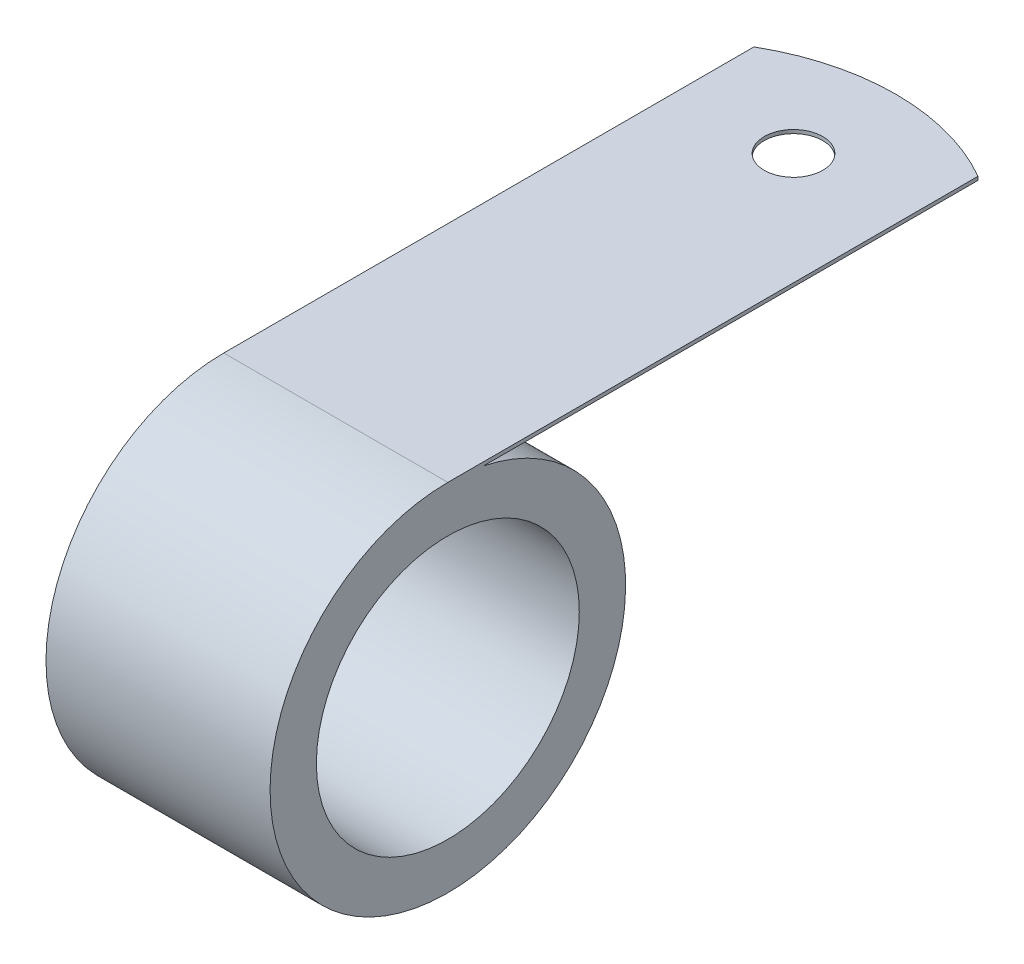
SolidWorks part; units mm, degrees
ref_plane "Front" through (0, 0, 0) normal (0, 0, 1) x (1, 0, 0)
ref_plane "Top" through (0, 0, 0) normal (0, 1, 0) x (1, 0, 0)
ref_plane "Right" through (0, 0, 0) normal (1, 0, 0) x (0, 0, -1)
sketch "Sketch1" plane through (0, 0, 0) normal (1, 0, 0) x (0, 0, -1)
  line L0 (0, 15.113) -> (47.625, 15.113)
  line L1 (3.0199, 14.8082) -> (47.625, 14.8082)
  line L2 (47.625, 14.8082) -> (47.625, 15.113)
  line L3 (0, 15.113) -> (0, -15.113) construction
  circle A0 centre (0, 0) radius 11.176
  arc A1 (0, 15.113) -> (3.0199, 14.8082) centre (0, 0) ccw
  dimension "D2" = 47.625
extrude "Boss-Extrude1" add sketch "Sketch1" along normal mid plane 19.05
sketch "Sketch2" plane through (0, 15.113, 0) normal (0, 1, 0) x (1, 0, 0)
  line L0 (0, 28.575) -> (0, 47.625) construction
  line L1 (9.525, 47.625) -> (-9.525, 47.625) construction
  line L2 (-9.525, 45.0728) -> (-9.525, 48.26)
  line L3 (-9.525, 47.625) -> (-9.525, 0) construction
  line L4 (-9.525, 48.26) -> (9.525, 48.26)
  line L5 (9.525, 45.0728) -> (9.525, 48.26)
  line L6 (9.525, 47.625) -> (9.525, 0) construction
  arc A0 (9.525, 45.0728) -> (-9.525, 45.0728) centre (0, 28.575) ccw
  circle A1 centre (0, 38.9128) radius 2.4892
  dimension "D2" = 0.635
extrude "OneHole" cut sketch "Sketch2" against normal up to next
sketch "Sketch4" plane through (0, 15.113, 0) normal (0, 1, 0) x (1, 0, 0)
  line L0 (0, 47.625) -> (0, 38.9128) construction
  line L2 (9.525, 38.9128) -> (-9.525, 38.9128) construction
  circle A0 centre (-9.525, 38.9128) radius 2.4892
  circle A1 centre (9.525, 38.9128) radius 2.4892
  dimension "D1" = 4.9784
  dimension "D2" = 8.7122
  dimension "D3" = 19.05
extrude "TwoHole" [suppressed] cut sketch "Sketch4" against normal up to next
equation "\"D2@Sketch1\"=\"Width@Boss-Extrude1\"*2.5"
equation "\"D1@Sketch4\" = \"HoleDia@Sketch2\""
equation "\"D2@Sketch4\" = \"HolePosition@Sketch2\""
